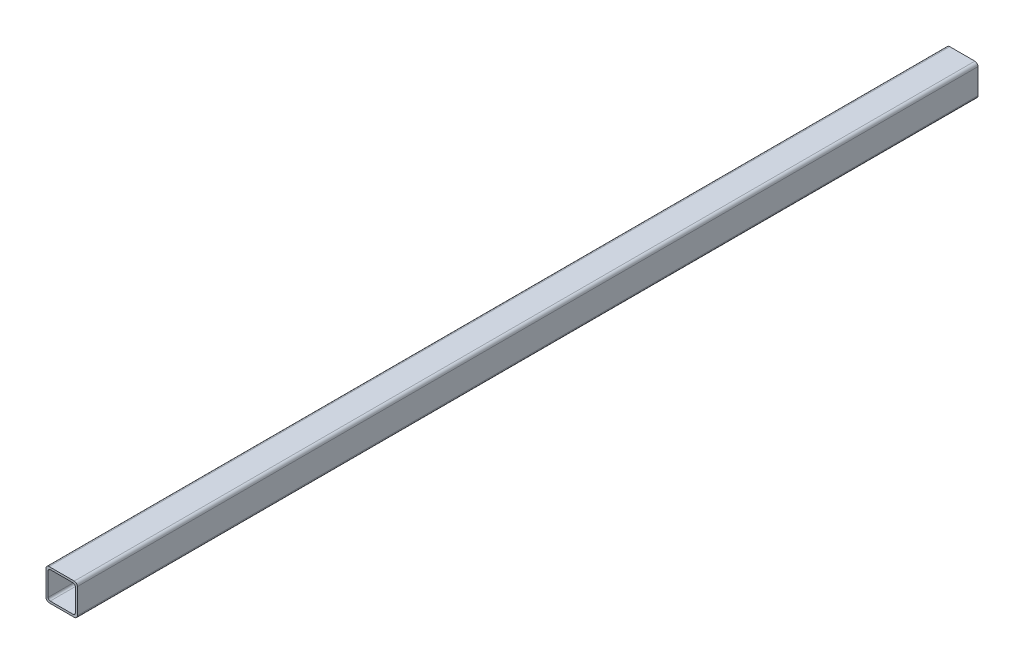
SolidWorks part; units mm, degrees
material "AISI 1020"
ref_plane "Спереди" through (0, 0, 0) normal (0, 0, 1) x (1, 0, 0)
ref_plane "Сверху" through (0, 0, 0) normal (0, 1, 0) x (1, 0, 0)
ref_plane "Справа" through (0, 0, 0) normal (1, 0, 0) x (0, 0, -1)
sketch "Эскиз1" plane through (0, 0, 0) normal (0, 0, 1) x (1, 0, 0)
  line L0 (-233, 0) -> (1317, 0) construction
  line B0 (-27, 0) -> (-3, 0)
  line B1 (-30, -3) -> (-30, -27)
  line B2 (-27, -30) -> (-3, -30)
  line B3 (0, -3) -> (0, -27)
  line B4 (-26, -2) -> (-4, -2)
  line B5 (-28, -4) -> (-28, -26)
  line B6 (-26, -28) -> (-4, -28)
  line B7 (-2, -4) -> (-2, -26)
  arc B8 (-30, -27) -> (-27, -30) centre (-27, -27) ccw
  arc B9 (-3, -30) -> (0, -27) centre (-3, -27) ccw
  arc B10 (-3, 0) -> (0, -3) centre (-3, -3) cw
  arc B11 (-27, 0) -> (-30, -3) centre (-27, -3) ccw
  arc B12 (-28, -26) -> (-26, -28) centre (-26, -26) ccw
  arc B13 (-4, -28) -> (-2, -26) centre (-4, -26) ccw
  arc B14 (-4, -2) -> (-2, -4) centre (-4, -4) cw
  arc B15 (-26, -2) -> (-28, -4) centre (-26, -4) ccw
sketch_block_instance "Блок-30х30х2-1"
sketch_block "Блок-30х30х2" parameters "D3"=3, "D4"=2, "D1"=30, "D2"=2
extrude "Бобышка-Вытянуть1" add sketch "Эскиз1" along normal up to surface (430 mm away)
mirror "Зеркальное отражение1" about plane through (-27, -27, 0) normal (0, 0, 1) of bodies 103
